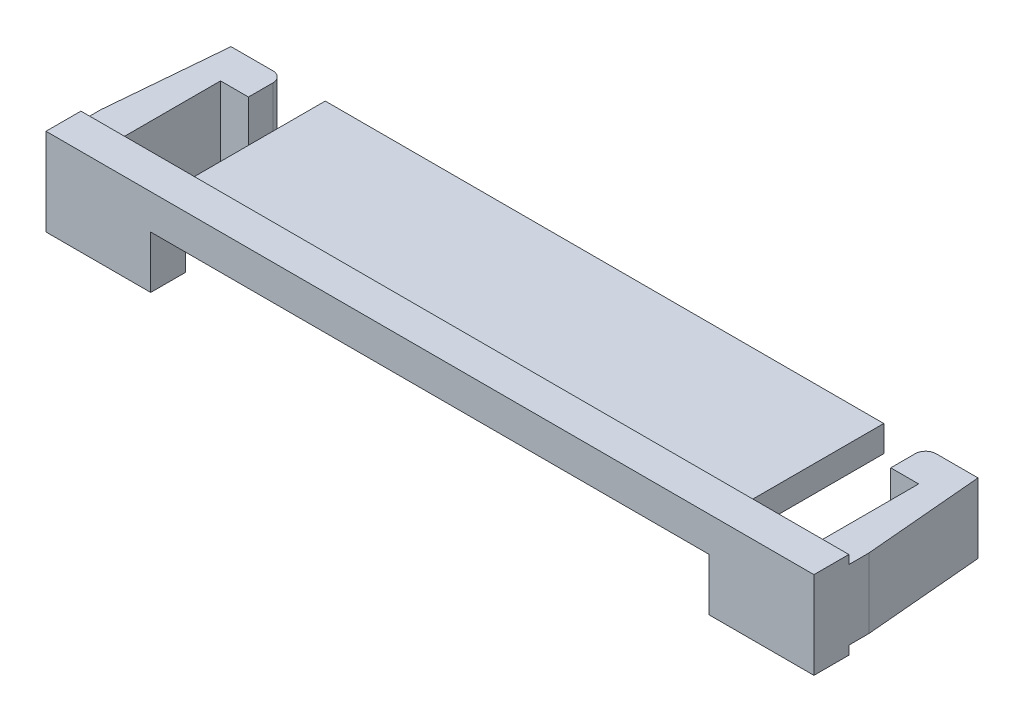
SolidWorks part; units mm, degrees
ref_plane "Front Plane" through (0, 0, 0) normal (0, 0, 1) x (1, 0, 0)
ref_plane "Top Plane" through (0, 0, 0) normal (0, 1, 0) x (1, 0, 0)
ref_plane "Right Plane" through (0, 0, 0) normal (1, 0, 0) x (0, 0, -1)
sketch "Sketch1" plane through (0, 0, 0) normal (0, 0, 1) x (1, 0, 0)
  line L1 (-11, 1.25) -> (11, 1.25)
  line L2 (-11, 1.25) -> (-11, -1.25)
  line L3 (-11, -1.25) -> (11, -1.25)
  line L4 (11, 1.25) -> (11, -1.25)
  line L5 (-11, 1.25) -> (11, -1.25) construction
  line L6 (-11, -1.25) -> (11, 1.25) construction
  point P0 (0, 0)
  dimension "D1" = 22
  dimension "D2" = 2.5
extrude "Boss-Extrude1" add sketch "Sketch1" along normal blind 5
sketch "Sketch2" plane through (0, 0, 0) normal (0, 0, -1) x (-1, 0, 0)
  line L0 (11, 1.25) -> (11, -1.25) construction
  line L1 (-11, 1.25) -> (11, 1.25)
  line L2 (-11, 1.25) -> (-11, 1)
  line L3 (-11, 1) -> (11, 1)
  line L4 (11, 1.25) -> (11, 1)
  line L5 (-11, -1.25) -> (-11, 1.25) construction
  line L6 (11, -1.25) -> (-11, -1.25)
  line L7 (11, -1.25) -> (11, -1)
  line L8 (11, -1) -> (-11, -1)
  line L9 (-11, -1.25) -> (-11, -1)
  dimension "D1" = 0.25
  dimension "D2" = 0.25
extrude "Cut-Extrude1" cut sketch "Sketch2" against normal blind 4
sketch "Sketch3" plane through (0, 0, 0) normal (0, 0, -1) x (-1, 0, 0)
  line L0 (-11, 1) -> (11, 1) construction
  line L1 (-10, 1) -> (-8, 1)
  line L2 (-10, 1) -> (-10, -1)
  line L3 (-10, -1) -> (-8, -1)
  line L4 (-8, 1) -> (-8, -1)
  line L5 (11, -1) -> (-11, -1) construction
  line L6 (-11, -1) -> (-11, 1) construction
  line L7 (10, 1) -> (8, 1)
  line L8 (10, 1) -> (10, -1)
  line L9 (10, -1) -> (8, -1)
  line L10 (8, 1) -> (8, -1)
  line L11 (11, 1) -> (11, -1) construction
  dimension "D1" = 1
  dimension "D2" = 1
  dimension "D3" = 2
  dimension "D4" = 2
extrude "Cut-Extrude2" cut sketch "Sketch3" against normal blind 4
sketch "Sketch5" plane through (0, 0, 0) normal (0, 0, -1) x (-1, 0, 0)
  line L0 (-8, -1) -> (-8, 1) construction
  line L1 (-8, 0.25) -> (8, 0.25)
  line L2 (-8, 0.25) -> (-8, -1.25)
  line L3 (-8, -1.25) -> (8, -1.25)
  line L4 (8, 0.25) -> (8, -1.25)
  line L5 (-11, -1.25) -> (11, -1.25) construction
  line L6 (8, 1) -> (8, -1) construction
  line L7 (11, 1.25) -> (-11, 1.25) construction
  dimension "D1" = 1
extrude "Cut-Extrude3" cut sketch "Sketch5" against normal blind 5
sketch "Sketch6" plane through (0, 1, 0) normal (0, 1, 0) x (1, 0, 0)
  line L1 (-11, 0) -> (-9.2, 0)
  line L2 (-11, 0) -> (-11, -1)
  line L3 (-11, -1) -> (-9.2, -1)
  line L4 (-9.2, 0) -> (-9.2, -1)
  line L5 (11, 0) -> (9.2, 0)
  line L6 (11, 0) -> (11, -1)
  line L7 (11, -1) -> (9.2, -1)
  line L8 (9.2, 0) -> (9.2, -1)
  dimension "D1" = 1.8
  dimension "D2" = 1.8
  dimension "D3" = 1
  dimension "D4" = 1
extrude "Boss-Extrude2" add sketch "Sketch6" against normal blind 2
fillet "Fillet1" radius 0.3 2 edges at (9.2, 0, 0) (-9.2, 0, 0)
chamfer "Chamfer1" distance 0.3 angle 85 2 edges at (11, 0, 0) (-11, 0, 0)
